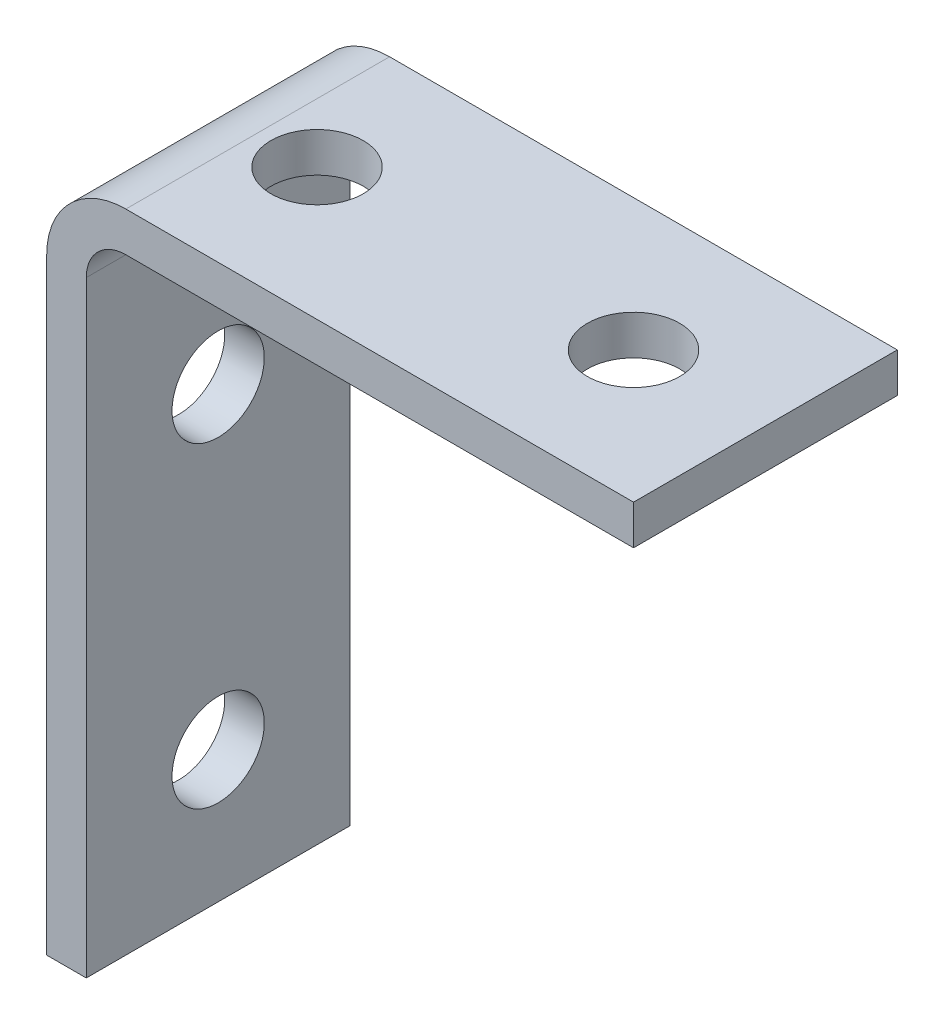
SolidWorks part; units mm, degrees
ref_plane "Front Plane" through (0, 0, 0) normal (0, 0, 1) x (1, 0, 0)
ref_plane "Top Plane" through (0, 0, 0) normal (0, 1, 0) x (1, 0, 0)
ref_plane "Right Plane" through (0, 0, 0) normal (1, 0, 0) x (0, 0, -1)
sketch "Sketch1" plane through (0, 0, 0) normal (0, 0, 1) x (1, 0, 0)
  line L0 (0, 0) -> (89, 0)
  line L1 (89, 0) -> (89, 104)
  line L2 (89, 104) -> (0, 104)
  line L3 (0, 104) -> (0, 0)
extrude "Boss-Extrude1" add sketch "Sketch1" against normal blind 40
sketch "Sketch2" plane through (0, 0, -40) normal (0, 0, -1) x (-1, 0, 0)
  line L0 (-6, 0) -> (-6, 98)
  line L1 (-6, 98) -> (-89, 98)
  line L2 (-89, 98) -> (-89, 0)
  line L3 (-89, 0) -> (-6, 0)
extrude "Cut-Extrude1" cut sketch "Sketch2" against normal through all
hole_wizard "Ø14.0 (14) Diameter Hole1" positions "Sketch4" profile "Sketch3" hole size "Ø14.0" standard "ANSI Metric"
sketch "Sketch4" plane through (0, 0, 0) normal (-1, 0, 0) x (0, 0, 1)
  point P0 (-20, 68)
  point P1 (-20, 20)
sketch "Sketch3" plane through (0, 68, -20) normal (0, 1, 0) x (0, 0, 1)
  line L0 (0, 0) -> (0, 89)
  line L1 (0, 89) -> (7, 89)
  line L2 (7, 89) -> (7, 0)
  line L5 (7, 0) -> (0, 0)
  line L11 (0, -6.35) -> (0, 107.95) construction
  dimension "Thru Hole Dia." = 14
  dimension "Thru Hole Depth" = 89
hole_wizard "Ø14.0 (14) Diameter Hole2" positions "Sketch6" profile "Sketch5" hole size "Ø14.0" standard "ANSI Metric"
sketch "Sketch6" plane through (0, 98, 0) normal (0, -1, 0) x (-1, 0, 0)
  point P0 (-69, 20)
  point P1 (-21, 20)
sketch "Sketch5" plane through (69, 98, -20) normal (1, 0, 0) x (0, 0, -1)
  line L0 (0, 0) -> (0, 6)
  line L1 (0, 6) -> (7, 6)
  line L2 (7, 6) -> (7, 0)
  line L5 (7, 0) -> (0, 0)
  line L11 (0, -6.35) -> (0, 107.95) construction
  dimension "Thru Hole Dia." = 14
  dimension "Thru Hole Depth" = 6
fillet "Fillet1" radius 6 1 edges at (6, 98, -20)
fillet "Fillet2" radius 12 1 edges at (0, 104, -20)
